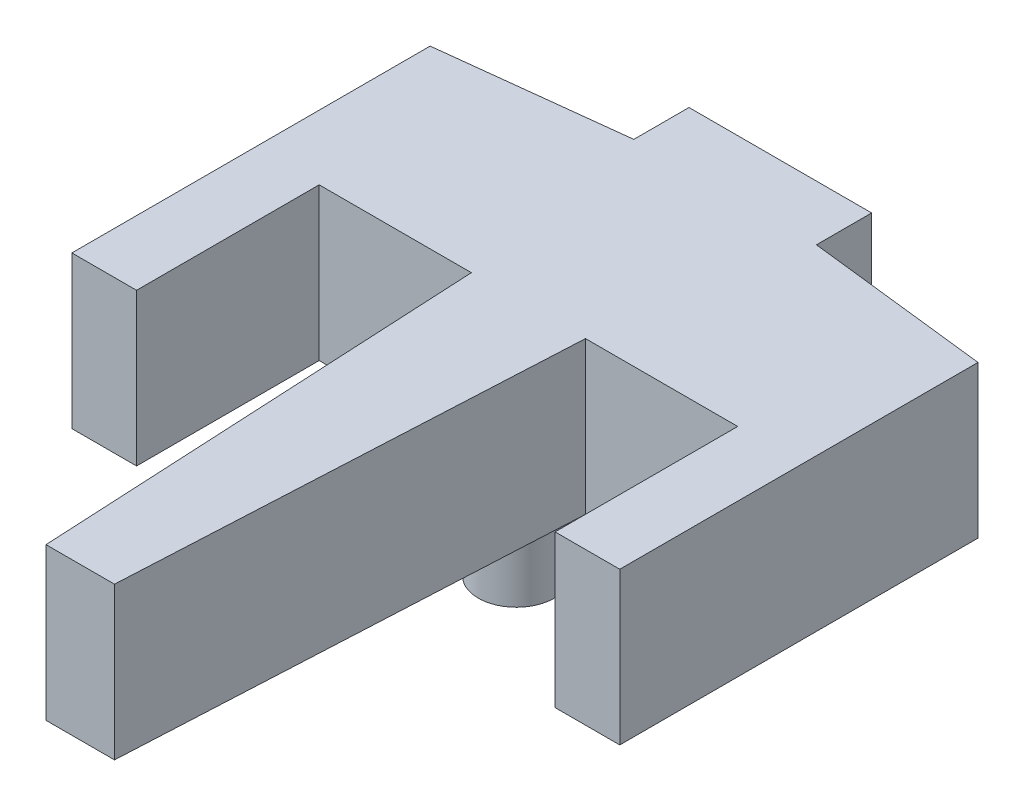
SolidWorks part; units mm, degrees
ref_plane "Front Plane" through (0, 0, 0) normal (0, 0, 1) x (1, 0, 0)
ref_plane "Top Plane" through (0, 0, 0) normal (0, 1, 0) x (1, 0, 0)
ref_plane "Right Plane" through (0, 0, 0) normal (1, 0, 0) x (0, 0, -1)
sketch "Sketch1" plane through (0, 0, 0) normal (0, 1, 0) x (1, 0, 0)
  line L0 (211.9879, 556.6422) -> (860.1786, 499.9329) construction
  line L1 (21.2777, 48.0579) -> (33.2777, 48.0579)
  line L2 (33.2777, 48.0579) -> (33.2777, 44.4311)
  line L3 (33.2777, 44.4311) -> (45.2777, 43.0465)
  line L4 (45.2777, 43.0465) -> (45.2777, 19.5078)
  line L5 (45.2777, 19.5078) -> (41.0277, 19.5078)
  line L6 (41.0277, 19.5078) -> (41.0277, 31.5078)
  line L7 (41.0277, 31.5078) -> (31.0277, 31.5078)
  line L8 (31.0277, 31.5078) -> (29.5277, 2.0579)
  line L9 (29.5277, 2.0579) -> (25.0277, 2.0579)
  line L10 (25.0277, 2.0579) -> (23.5277, 31.5078)
  line L11 (23.5277, 31.5078) -> (13.5277, 31.5078)
  line L12 (13.5277, 31.5078) -> (13.5277, 19.5078)
  line L13 (13.5277, 19.5078) -> (9.2777, 19.5078)
  line L14 (9.2777, 19.5078) -> (9.2777, 43.0465)
  line L15 (9.2777, 43.0465) -> (21.2777, 44.4311)
  line L16 (21.2777, 44.4311) -> (21.2777, 48.0579)
  dimension "D1" = 36
  dimension "D2" = 46
  dimension "D3" = 12
  dimension "D4" = 23.5387
  dimension "D5" = 23.5387
  dimension "D6" = 11.5
  dimension "D7" = 12
  dimension "D8" = 12
  dimension "D9" = 4.25
  dimension "D10" = 4.25
  dimension "D11" = 11.5
  dimension "D12" = 10
  dimension "D13" = 10
  dimension "D14" = 12
  dimension "D15" = 12
extrude "Boss-Extrude1" add sketch "Sketch1" along normal blind 10
sketch "Sketch2" plane through (0, 0, 0) normal (0, -1, 0) x (-1, 0, 0)
  line L0 (-23.5277, 31.5078) -> (-25.0277, 2.0579) construction
  line L3 (-29.5277, 2.0579) -> (-31.0277, 31.5078) construction
  circle A0 centre (-27.2777, 30.7119) radius 2.5
  dimension "D1" = 3.7047
  dimension "D3" = 5
  dimension "D2" = 3.7047
extrude "Boss-Extrude2" add sketch "Sketch2" along normal blind 5
